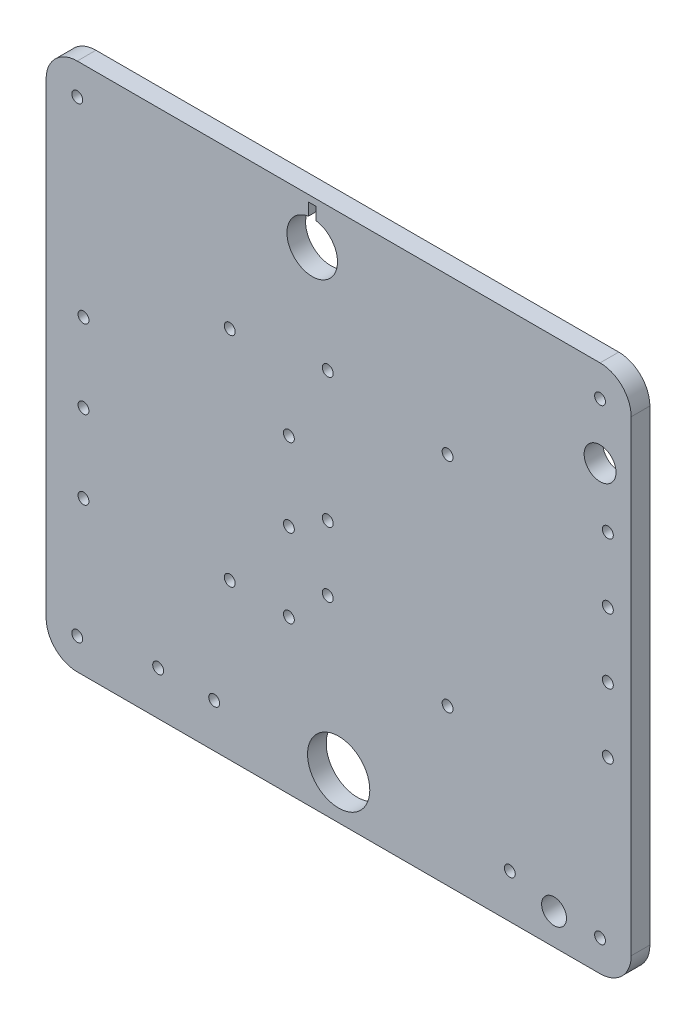
SolidWorks part; units mm, degrees
ref_plane "Plan de face" through (0, 0, 0) normal (0, 0, 1) x (1, 0, 0)
ref_plane "Plan de dessus" through (0, 0, 0) normal (0, 1, 0) x (1, 0, 0)
ref_plane "Plan de droite" through (0, 0, 0) normal (1, 0, 0) x (0, 0, -1)
sketch "Esquisse1" plane through (0, 0, 0) normal (0, 0, 1) x (1, 0, 0)
  line L0 (-94, -75) -> (-94, 75)
  line L1 (84, -75) -> (-84, -75) construction
  line L2 (84, -75) -> (84, 75) construction
  line L3 (84, 75) -> (-84, 75) construction
  line L4 (-84, -75) -> (-84, 75) construction
  line L5 (-16, -10.5) -> (-3.5, -10.5) construction
  line L7 (84, 85) -> (-84, 85)
  line L8 (94, -75) -> (94, 75)
  line L9 (84, -85) -> (-84, -85)
  line L10 (-94, -85) -> (-94, 85) construction
  line L11 (94, -85) -> (-94, -85) construction
  line L12 (94, -85) -> (94, 85) construction
  line L13 (94, 85) -> (-94, 85) construction
  line L20 (-3.5, -10.5) -> (-3.5, -2.625) construction
  line L21 (0, -70.9) -> (0, -75) construction
  line L27 (-11, -30.7) -> (-11, -28.5) construction
  line L28 (-35, 35) -> (35, 35) construction
  line L29 (-35, 35) -> (-35, -35) construction
  line L30 (-35, -35) -> (35, -35) construction
  line L32 (-11, -25) -> (-11, -22) construction
  line L33 (-12.75, -30.7) -> (-24.8305, -30.7) construction
  line L34 (8, -28.5) -> (-7.5, -28.5) construction
  line L35 (35, 35) -> (35, -35) construction
  line L36 (-21, 74.1) -> (-21, -55.9) construction
  line L37 (-9.75, 78.9283) -> (-9.75, 82.9283)
  line L38 (-9.75, 82.9283) -> (-7.25, 82.9283)
  line L39 (-7.25, 82.9283) -> (-7.25, 78.9283)
  line L40 (55, -70.9) -> (69.2102, -75) construction
  line L41 (69.2102, -75) -> (84, -75) construction
  circle A0 centre (-84, 75) radius 1.75
  circle A1 centre (84, 75) radius 1.75
  circle A2 centre (84, -75) radius 1.75
  circle A3 centre (-84, -75) radius 1.75
  arc A4 (-94, -75) -> (-84, -85) centre (-84, -75) ccw
  arc A5 (94, -75) -> (84, -85) centre (84, -75) cw
  arc A6 (84, 85) -> (94, 75) centre (84, 75) cw
  arc A7 (-94, 75) -> (-84, 85) centre (-84, 75) cw
  circle A41 centre (-82, -35.7) radius 1.75
  circle A42 centre (-82, -10.5) radius 1.75
  circle A43 centre (-82, 14.7) radius 1.75
  circle A44 centre (-16, -35.7) radius 1.75
  circle A45 centre (-3.5, -23.5) radius 1.75
  circle A46 centre (86.5, -23.5) radius 1.75
  circle A47 centre (86.5, -2.625) radius 1.75
  circle A48 centre (86.5, 18.25) radius 1.75
  circle A49 centre (86.5, 39.125) radius 1.75
  circle A50 centre (-3.5, -2.625) radius 1.75
  circle A51 centre (-3.5, 39.125) radius 1.75
  circle A52 centre (-16, -10.5) radius 1.75
  circle A53 centre (-16, 14.7) radius 1.75
  circle A64 centre (-58, -70.9) radius 1.75
  circle A65 centre (-40, -70.9) radius 1.75
  circle A66 centre (-40, -70.9) radius 1.75 construction
  circle A67 centre (55, -70.9) radius 1.75
  circle A68 centre (0, 0) radius 40 construction
  circle A75 centre (0, 0) radius 34.5 construction
  circle A76 centre (-35, 35) radius 1.75
  circle A77 centre (35, 35) radius 1.75
  circle A78 centre (35, -35) radius 1.75
  circle A79 centre (-35, -35) radius 1.75
  circle A80 centre (0, -70.9) radius 10
  arc A81 (-9.75, 78.9283) -> (-7.25, 78.9283) centre (-8.5, 70.9) ccw
  circle A82 centre (84, 57.0625) radius 5.125
  circle A85 centre (69.2102, -75) radius 4
  point P7 (0, 85)
  point P28 (-94, 0)
  point P61 (0, 35)
  point P62 (-35, 0)
  point P112 (-8.5, 82.9283)
  point P113 (0, 0)
  dimension "D3" = 3.5
  dimension "D5" = 10
  dimension "D7" = 3.5
  dimension "D11" = 113
  dimension "D10" = 70
  dimension "D15" = 4.1
  dimension "D12" = 20
  dimension "D14" = 16.25
  dimension "D17" = 10.25
  dimension "D8" = 3
  dimension "D18" = 17.9375
  dimension "D6" = 80
  dimension "D22" = 8
  dimension "D1" = 150
  dimension "D2" = 168
  dimension "D4" = 10
  dimension "D9" = 25.2
  dimension "D13" = 5.5
  dimension "D16" = 12.5
  dimension "D20" = 4
  dimension "D21" = 2.5
extrude "Boss.-Extru.1" add sketch "Esquisse1" along normal blind 6
